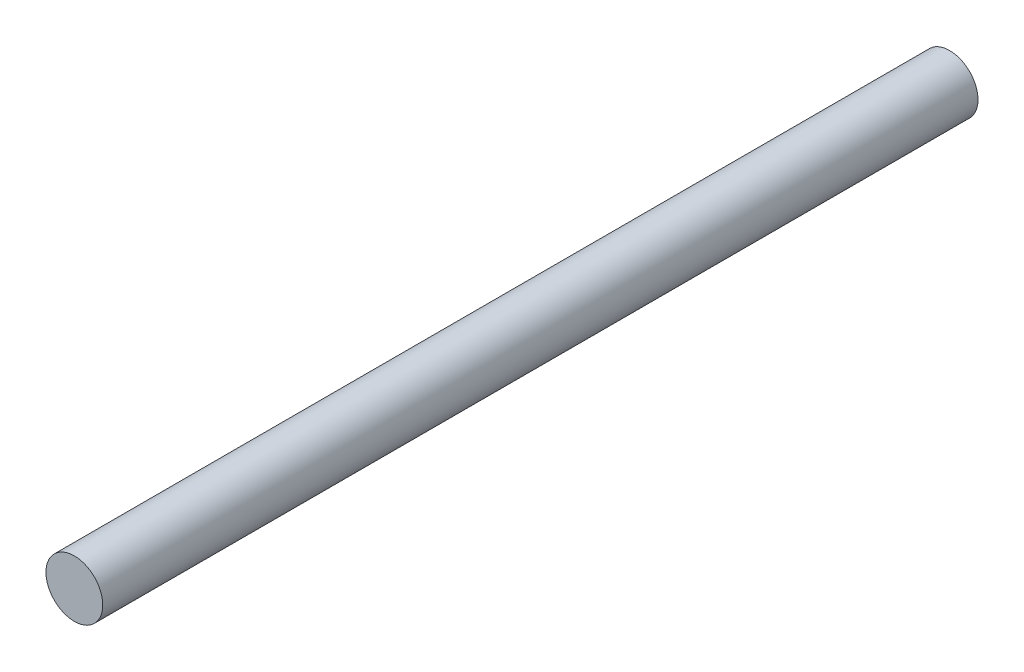
SolidWorks part; units mm, degrees
ref_plane "Ön Düzlem" through (0, 0, 0) normal (0, 0, 1) x (1, 0, 0)
ref_plane "Üst Düzlem" through (0, 0, 0) normal (0, 1, 0) x (1, 0, 0)
ref_plane "Sağ Düzlem" through (0, 0, 0) normal (1, 0, 0) x (0, 0, -1)
sketch "Çizim1" plane through (0, 0, 0) normal (0, 0, 1) x (1, 0, 0)
  circle A0 centre (0, 0) radius 6
extrude "Yükseklik-Ekstrüzyon1" add sketch "Çizim1" along normal blind 185
